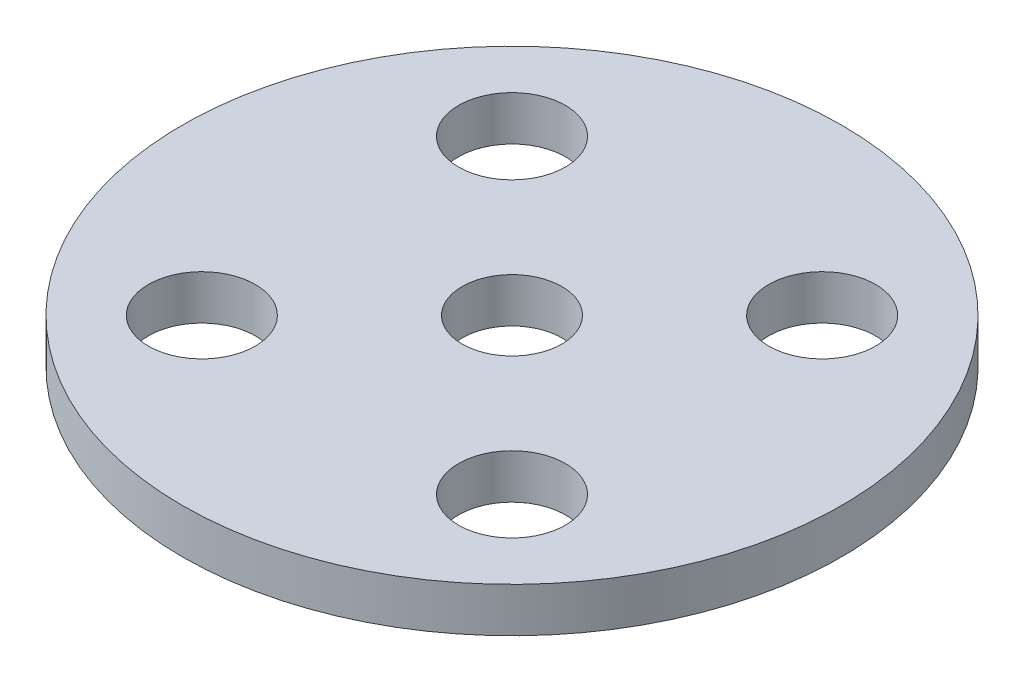
SolidWorks part; units mm, degrees
ref_plane "Front Plane" through (0, 0, 0) normal (0, 0, 1) x (1, 0, 0)
ref_plane "Top Plane" through (0, 0, 0) normal (0, 1, 0) x (1, 0, 0)
ref_plane "Right Plane" through (0, 0, 0) normal (1, 0, 0) x (0, 0, -1)
sketch "Sketch1" plane through (0, 0, 0) normal (0, 1, 0) x (1, 0, 0)
  line L5 (13.5959, -13.5959) -> (-13.5959, 13.5959) construction
  line L6 (13.5959, 13.5959) -> (-13.5959, -13.5959) construction
  circle A0 centre (-11.0559, 11.0559) radius 3.81
  circle A4 centre (0, 0) radius 3.556
  circle A5 centre (11.0559, -11.0559) radius 3.81
  circle A6 centre (11.0559, 11.0559) radius 3.81
  circle A7 centre (-11.0559, -11.0559) radius 3.81
  circle A8 centre (0, 0) radius 23.495
  point P0 (0, 0)
  point P17 (-15.9684, 0)
  point P20 (0, 0)
  dimension "D2" = 7.62
  dimension "D5" = 7.112
  dimension "D6" = 7.62
  dimension "D1" = 46.99
  dimension "D4" = 31.2707
  dimension "D7" = 2
extrude "Boss-Extrude1" add sketch "Sketch1" along normal blind 3.175
